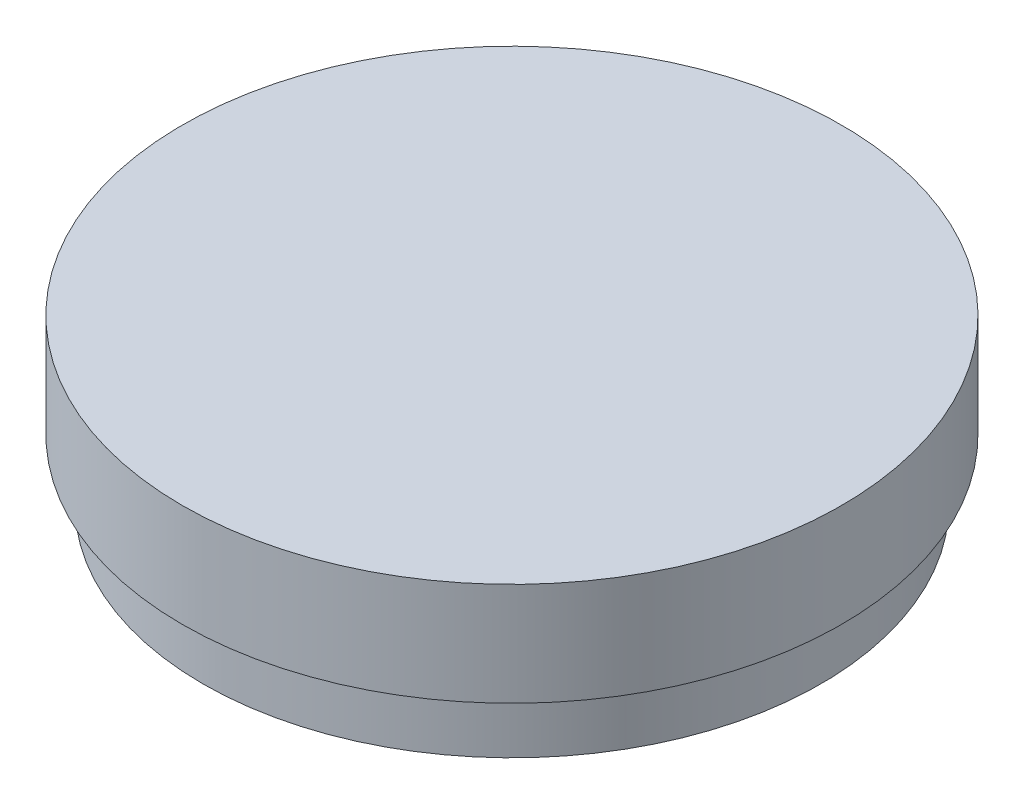
SolidWorks part; units mm, degrees
ref_plane "Front Plane" through (0, 0, 0) normal (0, 0, 1) x (1, 0, 0)
ref_plane "Top Plane" through (0, 0, 0) normal (0, 1, 0) x (1, 0, 0)
ref_plane "Right Plane" through (0, 0, 0) normal (1, 0, 0) x (0, 0, -1)
sketch "Sketch1" plane through (0, 0, 0) normal (0, 1, 0) x (1, 0, 0)
  circle A0 centre (0, 0) radius 15
  dimension "D1" = 30
extrude "Boss-Extrude1" add sketch "Sketch1" along normal blind 3
sketch "Sketch2" plane through (0, 3, 0) normal (0, 1, 0) x (1, 0, 0)
  circle A2 centre (0, 0) radius 16
  circle A3 centre (0, 0) radius 16
  dimension "D1" = 1
extrude "Boss-Extrude2" add sketch "Sketch2" along normal blind 5
